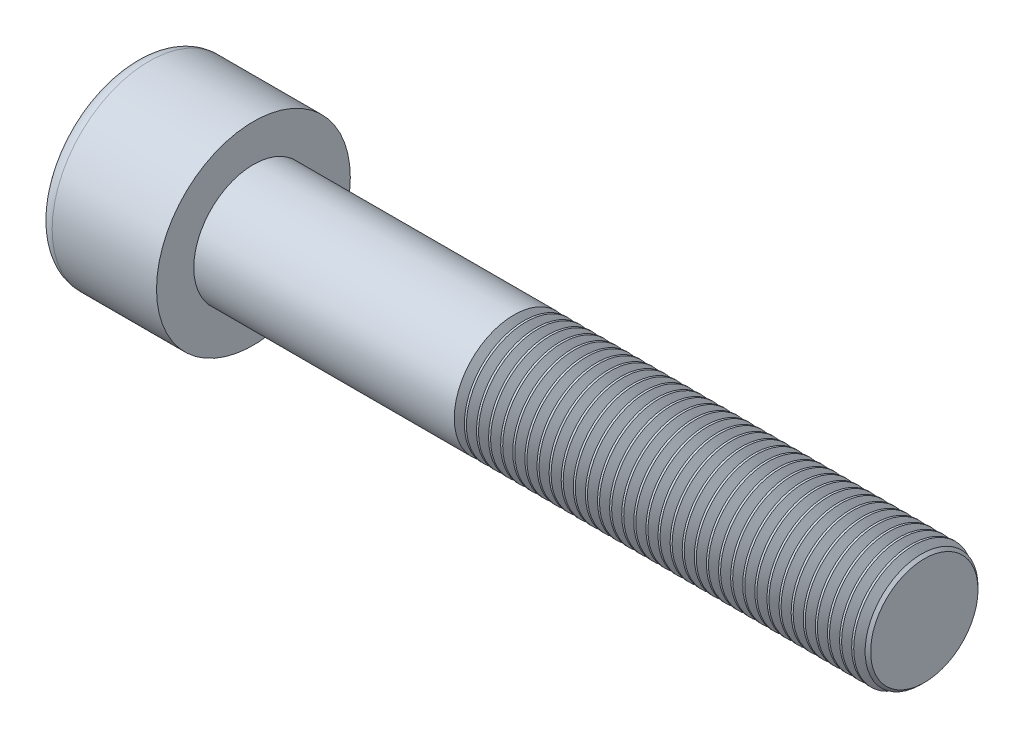
SolidWorks part; units mm, degrees
ref_plane "Front" through (0, 0, 0) normal (0, 0, 1) x (1, 0, 0)
ref_plane "Top" through (0, 0, 0) normal (0, 1, 0) x (1, 0, 0)
ref_plane "Right" through (0, 0, 0) normal (1, 0, 0) x (0, 0, -1)
sketch "Sketch1" plane through (0, 0, 0) normal (1, 0, 0) x (0, 0, -1)
  circle A0 centre (0, 0) radius 6.5
  dimension "dk" = 13
extrude "BaseHead" add sketch "Sketch1" along normal blind 8
sketch "Sketch2" plane through (8, 0, 0) normal (1, 0, 0) x (0, 0, -1)
  circle A0 centre (0, 0) radius 4
  dimension "d" = 8
extrude "BaseBody" add sketch "Sketch2" along normal blind 45
cosmetic thread "ThreadCosmetic1" [suppressed] parameters "b"=28, "D2"=6.647
sketch "Sketch3" plane through (0, 0, 0) normal (1, 0, 0) x (0, 0, -1)
  line L1 (3.4641, 0) -> (1.7321, 3)
  line L2 (1.7321, 3) -> (-1.7321, 3)
  line L3 (-1.7321, 3) -> (-3.4641, 0)
  line L4 (-3.4641, 0) -> (-1.7321, -3)
  line L5 (-1.7321, -3) -> (1.7321, -3)
  line L6 (1.7321, -3) -> (3.4641, 0)
  circle A0 centre (0, 0) radius 3 construction
  dimension "s" = 6
  dimension "e" = 6.9282
extrude "HexagonSocket" cut sketch "Sketch3" along normal blind 4
sketch "Sketch4" plane through (-4.1961, 0.75, 0) normal (0, 0, 1) x (-1, 0, 0)
  line L0 (-8.1961, 3.75) -> (-9.9282, 0.75)
  line L2 (-9.9282, 0.75) -> (-8.1961, 0.75)
  line L3 (-8.1961, 0.75) -> (-8.1961, 3.75)
  line L4 (-5.0351, 0.75) -> (0.839, 0.75) construction
  line L5 (-57.1961, 0.75) -> (-12.1961, 0.75) construction
  line L6 (-12.1961, 0.75) -> (-4.1961, 0.75) construction
  dimension "m" = 60
revolve "Cut-Revolve1" cut sketch "Sketch4" angle 360 about L4
fillet "HeadFillet" [suppressed] radius 0.4
fillet "TopFillet" radius 1 1 edges at (0, 0, -6.5)
chamfer "Chamfer1" distance 0.4 angle 45 1 edges at (53, 0, -4)
sketch "Sketch5" plane through (0, 0, 0) normal (0, 0, 1) x (1, 0, 0)
  line L0 (52.6, 3.4141) -> (52.9383, 4)
  line L1 (52.9383, 4) -> (52.9383, 4.6765)
  line L2 (52.9383, 4.6765) -> (52.2618, 4.6765)
  line L3 (52.2618, 4.6765) -> (52.2618, 4)
  line L4 (52.2618, 4) -> (52.6, 3.4141)
  line L5 (0, 0) -> (7.8886, 0) construction
  line L6 (52.6, -4) -> (52.6, 4) construction
  dimension "D1" = 8
  dimension "D2" = 0.6765
revolve "Cut-Revolve10" cut sketch "Sketch5" angle 360 about L5
pattern_linear "LPattern10" count 34 spacing 0.8118 along (-1, 0, 0) of "Cut-Revolve10"
equation "\"r1@TopFillet\" = \"d@Sketch2\" / 8"
equation "\"D1@Chamfer1\" = \"r@HeadFillet\""
equation "\"D1@Sketch5\" = \"d@Sketch2\""
equation "\"D2@Sketch5\" =  ( \"d@Sketch2\" - \"D2@ThreadCosmetic1\" )  / 2"
equation "\"D3@LPattern10\" = \"D2@Sketch5\" * 1.2"
equation "\"D1@LPattern10\" = \"b@ThreadCosmetic1\" / \"D3@LPattern10\""
